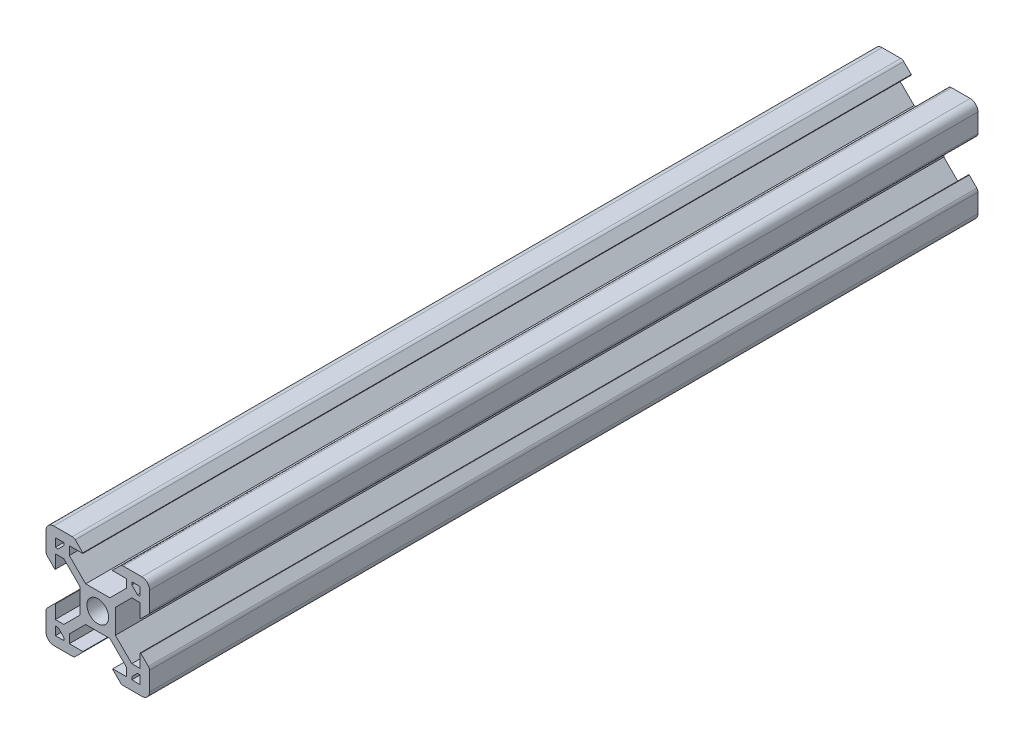
SolidWorks part; units mm, degrees
ref_plane "Front Plane" through (0, 0, 0) normal (0, 0, 1) x (1, 0, 0)
ref_plane "Top Plane" through (0, 0, 0) normal (0, 1, 0) x (1, 0, 0)
ref_plane "Right Plane" through (0, 0, 0) normal (1, 0, 0) x (0, 0, -1)
sketch "Sketch2" plane through (0, 0, 0) normal (0, 0, 1) x (1, 0, 0)
  line L0 (-8.2, 2.89) -> (-8.2, 5.5)
  line L1 (-2.1, 0) -> (-10, 0) construction
  line L2 (0, 2.1) -> (0, 10) construction
  line L3 (-4.9072, 10) -> (-8.5, 10)
  line L4 (-10, 4.9072) -> (-10, 8.5)
  line L5 (-2.1, 0) -> (-3.4, 0) construction
  line L6 (0, 2.1) -> (0, 3.4) construction
  line L7 (0, 3.4) -> (-2.3393, 3.4)
  line L8 (-3.4, 0) -> (-3.4, 2.3393)
  line L9 (-2.89, 8.2) -> (-5.5, 8.2)
  line L10 (-6.57, 8.2) -> (-6.57, 7.66)
  line L11 (-8.2, 6.57) -> (-7.66, 6.57)
  line L12 (-5.5, 8.2) -> (-5.5, 6.5607)
  line L13 (-6.5607, 5.5) -> (-8.2, 5.5)
  line L14 (-8.2, 8.2) -> (-1.4849, 1.4849) construction
  line L15 (-6.5607, 5.5) -> (-3.4, 2.3393)
  line L16 (-5.5, 6.5607) -> (-2.3393, 3.4)
  line L17 (-7.66, 6.57) -> (-6.57, 7.66)
  line L18 (-8.7303, 7.6697) -> (-0.5303, -0.5303) construction
  line L19 (-7.6697, 8.7303) -> (0.5303, 0.5303) construction
  line L20 (-8.2, 8.2) -> (0, 0) construction
  line L21 (-8.2, 6.57) -> (-8.2, 8.2)
  line L22 (-8.2, 0) -> (-8.2, 8.2) construction
  line L23 (-6.57, 8.2) -> (-8.2, 8.2)
  line L24 (0, 8.2) -> (-8.2, 8.2) construction
  line L25 (-10, 0) -> (-10, 10) construction
  line L26 (0, 10) -> (-10, 10) construction
  line L27 (-2.89, 8.31) -> (-2.89, 8.2)
  line L29 (-8.31, 2.89) -> (-8.2, 2.89)
  line L30 (-4.3486, 9.7686) -> (-2.89, 8.31)
  line L31 (-8.31, 2.89) -> (-9.7686, 4.3486)
  arc A0 (0, 2.1) -> (-2.1, 0) centre (0, 0) ccw
  arc A1 (-10, 8.5) -> (-8.5, 10) centre (-8.5, 8.5) cw
  arc A2 (-9.7686, 4.3486) -> (-10, 4.9072) centre (-9.21, 4.9072) cw
  arc A3 (-4.3486, 9.7686) -> (-4.9072, 10) centre (-4.9072, 9.21) ccw
  point P29 (-10, 10)
  point P39 (-10, 4.58)
  point P42 (-4.58, 10)
  dimension "D3" = 2.1
  dimension "D15" = 1.5
  dimension "D22" = 0.79
  dimension "D1" = 10
  dimension "D2" = 10
  dimension "D4" = 1.8
  dimension "D5" = 3.43
  dimension "D6" = 3.43
  dimension "D7" = 0.54
  dimension "D8" = 0.54
  dimension "D9" = 1.07
  dimension "D10" = 1.07
  dimension "D11" = 3.4
  dimension "D12" = 3.4
  dimension "D16" = 7.11
  dimension "D17" = 0.11
  dimension "D18" = 1.69
  dimension "D19" = 0.11
  dimension "D20" = 7.11
  dimension "D21" = 1.69
  dimension "D13" = 0.75
  dimension "D14" = 0.75
sketch "Sketch6" plane through (0, 0, 0) normal (0, 0, 1) x (1, 0, 0)
  line L0 (-3.4, 0) -> (-3.4, 2.3393) construction
  line L1 (-6.5607, 5.5) -> (-3.4, 2.3393) construction
  line L2 (-6.5607, 5.5) -> (-8.2, 5.5) construction
  line L3 (-8.2, 2.89) -> (-8.2, 5.5) construction
  line L4 (-8.31, 2.89) -> (-8.2, 2.89) construction
  line L5 (-7.66, 6.57) -> (-6.57, 7.66)
  line L6 (-6.57, 7.66) -> (-6.57, 8.2)
  line L7 (-6.57, 8.2) -> (-8.2, 8.2)
  line L8 (-8.2, 8.2) -> (-8.2, 6.57)
  line L9 (-8.2, 6.57) -> (-7.66, 6.57)
  line L10 (-7.66, 6.57) -> (-6.57, 7.66)
  line L11 (-6.57, 7.66) -> (-6.57, 8.2)
  line L12 (-6.57, 8.2) -> (-8.2, 8.2)
  line L13 (-8.2, 8.2) -> (-8.2, 6.57)
  line L14 (-8.2, 6.57) -> (-7.66, 6.57)
  line L15 (-8.31, 2.89) -> (-9.7686, 4.3486) construction
  line L16 (-10, 4.9072) -> (-10, 8.5) construction
  line L17 (-4.9072, 10) -> (-8.5, 10) construction
  line L18 (-4.3486, 9.7686) -> (-2.89, 8.31) construction
  line L19 (-2.89, 8.31) -> (-2.89, 8.2) construction
  line L20 (-2.89, 8.2) -> (-5.5, 8.2) construction
  line L21 (-5.5, 8.2) -> (-5.5, 6.5607) construction
  line L22 (-5.5, 6.5607) -> (-2.3393, 3.4) construction
  line L23 (0, 3.4) -> (-2.3393, 3.4) construction
  line L24 (-3.4, -2.3393) -> (-3.4, 2.3393)
  line L25 (-6.5607, 5.5) -> (-3.4, 2.3393)
  line L26 (-6.5607, 5.5) -> (-8.2, 5.5)
  line L27 (-8.2, 2.89) -> (-8.2, 5.5)
  line L28 (-8.31, 2.89) -> (-8.2, 2.89)
  line L29 (-8.31, 2.89) -> (-9.7686, 4.3486)
  line L30 (-10, 4.9072) -> (-10, 8.5)
  line L31 (-4.9072, 10) -> (-8.5, 10)
  line L32 (-4.3486, 9.7686) -> (-2.89, 8.31)
  line L33 (-2.89, 8.31) -> (-2.89, 8.2)
  line L34 (-2.89, 8.2) -> (-5.5, 8.2)
  line L35 (-5.5, 8.2) -> (-5.5, 6.5607)
  line L36 (-5.5, 6.5607) -> (-2.3393, 3.4)
  line L37 (2.3393, 3.4) -> (-2.3393, 3.4)
  line L38 (0, 2.1) -> (0, 10) construction
  line L39 (-2.1, 0) -> (-10, 0) construction
  line L40 (0, 2.1) -> (0, 10) construction
  line L41 (-2.1, 0) -> (-10, 0) construction
  line L42 (2.1, 0) -> (10, 0) construction
  line L43 (5.5, 6.5607) -> (2.3393, 3.4)
  line L44 (5.5, 8.2) -> (5.5, 6.5607)
  line L45 (2.89, 8.2) -> (5.5, 8.2)
  line L46 (2.89, 8.31) -> (2.89, 8.2)
  line L47 (4.3486, 9.7686) -> (2.89, 8.31)
  line L48 (4.9072, 10) -> (8.5, 10)
  line L49 (10, 4.9072) -> (10, 8.5)
  line L50 (8.31, 2.89) -> (9.7686, 4.3486)
  line L51 (8.31, 2.89) -> (8.2, 2.89)
  line L52 (8.2, 2.89) -> (8.2, 5.5)
  line L53 (6.5607, 5.5) -> (8.2, 5.5)
  line L54 (6.5607, 5.5) -> (3.4, 2.3393)
  line L55 (3.4, -2.3393) -> (3.4, 2.3393)
  line L56 (8.2, 6.57) -> (7.66, 6.57)
  line L57 (8.2, 8.2) -> (8.2, 6.57)
  line L58 (6.57, 8.2) -> (8.2, 8.2)
  line L59 (6.57, 7.66) -> (6.57, 8.2)
  line L60 (7.66, 6.57) -> (6.57, 7.66)
  line L61 (0, -2.1) -> (0, -10) construction
  line L62 (7.66, -6.57) -> (6.57, -7.66)
  line L63 (6.57, -7.66) -> (6.57, -8.2)
  line L64 (6.57, -8.2) -> (8.2, -8.2)
  line L65 (8.2, -8.2) -> (8.2, -6.57)
  line L66 (8.2, -6.57) -> (7.66, -6.57)
  line L67 (6.5607, -5.5) -> (3.4, -2.3393)
  line L68 (6.5607, -5.5) -> (8.2, -5.5)
  line L69 (8.2, -2.89) -> (8.2, -5.5)
  line L70 (8.31, -2.89) -> (8.2, -2.89)
  line L71 (8.31, -2.89) -> (9.7686, -4.3486)
  line L72 (10, -4.9072) -> (10, -8.5)
  line L73 (4.9072, -10) -> (8.5, -10)
  line L74 (4.3486, -9.7686) -> (2.89, -8.31)
  line L75 (2.89, -8.31) -> (2.89, -8.2)
  line L76 (2.89, -8.2) -> (5.5, -8.2)
  line L77 (5.5, -8.2) -> (5.5, -6.5607)
  line L78 (5.5, -6.5607) -> (2.3393, -3.4)
  line L79 (2.3393, -3.4) -> (-2.3393, -3.4)
  line L80 (-5.5, -6.5607) -> (-2.3393, -3.4)
  line L81 (-5.5, -8.2) -> (-5.5, -6.5607)
  line L82 (-2.89, -8.2) -> (-5.5, -8.2)
  line L83 (-2.89, -8.31) -> (-2.89, -8.2)
  line L84 (-4.3486, -9.7686) -> (-2.89, -8.31)
  line L85 (-4.9072, -10) -> (-8.5, -10)
  line L86 (-10, -4.9072) -> (-10, -8.5)
  line L87 (-8.31, -2.89) -> (-9.7686, -4.3486)
  line L88 (-8.31, -2.89) -> (-8.2, -2.89)
  line L89 (-8.2, -2.89) -> (-8.2, -5.5)
  line L90 (-6.5607, -5.5) -> (-8.2, -5.5)
  line L91 (-6.5607, -5.5) -> (-3.4, -2.3393)
  line L92 (-8.2, -6.57) -> (-7.66, -6.57)
  line L93 (-8.2, -8.2) -> (-8.2, -6.57)
  line L94 (-6.57, -8.2) -> (-8.2, -8.2)
  line L95 (-6.57, -7.66) -> (-6.57, -8.2)
  line L96 (-7.66, -6.57) -> (-6.57, -7.66)
  arc A0 (0, 2.1) -> (-2.1, 0) centre (0, 0) ccw construction
  arc A1 (-10, 4.9072) -> (-9.7686, 4.3486) centre (-9.21, 4.9072) ccw construction
  arc A2 (-8.5, 10) -> (-10, 8.5) centre (-8.5, 8.5) ccw construction
  arc A3 (-4.3486, 9.7686) -> (-4.9072, 10) centre (-4.9072, 9.21) ccw construction
  circle A4 centre (0, 0) radius 2.1
  arc A5 (-10, 4.9072) -> (-9.7686, 4.3486) centre (-9.21, 4.9072) ccw
  arc A6 (-8.5, 10) -> (-10, 8.5) centre (-8.5, 8.5) ccw
  arc A7 (-4.3486, 9.7686) -> (-4.9072, 10) centre (-4.9072, 9.21) ccw
  arc A8 (4.3486, 9.7686) -> (4.9072, 10) centre (4.9072, 9.21) cw
  arc A9 (8.5, 10) -> (10, 8.5) centre (8.5, 8.5) cw
  arc A10 (10, 4.9072) -> (9.7686, 4.3486) centre (9.21, 4.9072) cw
  arc A11 (10, -4.9072) -> (9.7686, -4.3486) centre (9.21, -4.9072) ccw
  arc A12 (8.5, -10) -> (10, -8.5) centre (8.5, -8.5) ccw
  arc A13 (4.3486, -9.7686) -> (4.9072, -10) centre (4.9072, -9.21) ccw
  arc A14 (-4.3486, -9.7686) -> (-4.9072, -10) centre (-4.9072, -9.21) cw
  arc A15 (-8.5, -10) -> (-10, -8.5) centre (-8.5, -8.5) cw
  arc A16 (-10, -4.9072) -> (-9.7686, -4.3486) centre (-9.21, -4.9072) cw
  point P85 (3.4, 0)
  dimension "D1" = 0
extrude "Boss-Extrude1" add sketch "Sketch6" against normal blind 160
